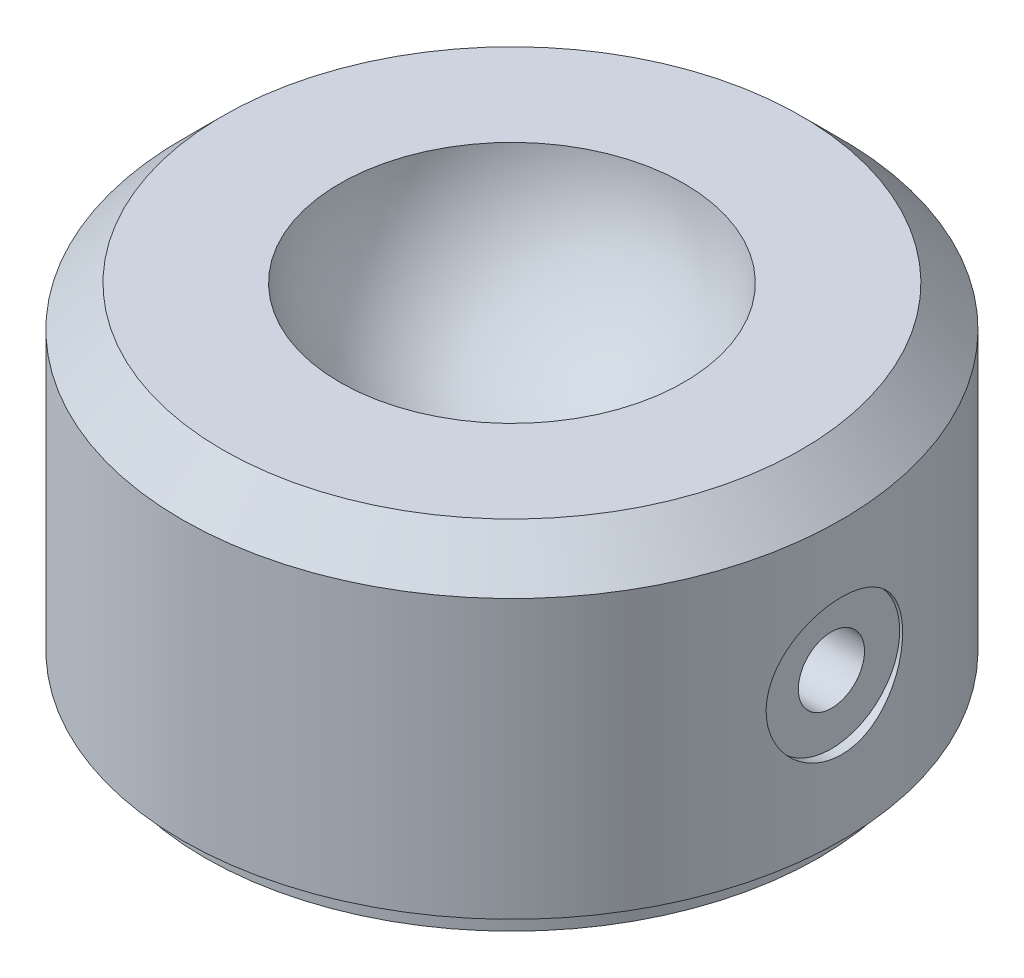
SolidWorks part; units mm, degrees
ref_plane "Front Plane" through (0, 0, 0) normal (0, 0, 1) x (1, 0, 0)
ref_plane "Top Plane" through (0, 0, 0) normal (0, 1, 0) x (1, 0, 0)
ref_plane "Right Plane" through (0, 0, 0) normal (1, 0, 0) x (0, 0, -1)
sketch "Sketch1" plane through (0, 0, 0) normal (0, 1, 0) x (1, 0, 0)
  circle A0 centre (0, 0) radius 12.446
  dimension "D1" = 24.892
extrude "Extrude1" add sketch "Sketch1" along normal mid plane 12.0142
chamfer "Chamfer1" distance 1.524 angle 45 1 edges at (0, 6.0071, 12.446)
sketch "Sketch2" plane through (0, -6.0071, 0) normal (0, -1, 0) x (1, 0, 0)
  circle A0 centre (0, 0) radius 11.5951
  dimension "D1" = 23.1902
extrude "Extrude2" add sketch "Sketch2" along normal blind 0.9908
sketch "Sketch3" plane through (0, 6.0071, 0) normal (0, 1, 0) x (1, 0, 0)
  circle A0 centre (0, 0) radius 1.5875
  dimension "D1" = 3.175
extrude "Extrude3" cut sketch "Sketch3" against normal blind 6.3754
sketch "Sketch4" plane through (0, 0, 0) normal (0, 0, 1) x (1, 0, 0)
  line L0 (0, 13.0351) -> (0, -0.0049)
  line L1 (10.922, 6.0071) -> (-10.922, 6.0071) construction
  arc A0 (0, 13.0351) -> (0, -0.0049) centre (0, 6.5151) cw
  dimension "D1" = 6.52
  dimension "D2" = 0.508
revolve "Cut-Revolve1" cut sketch "Sketch4" angle 360 about L0
ref_plane "Plane1" through (12.446, 0, 0) normal (1, 0, 0) x (0, 0, -1)
hole_wizard "5/16 (0.3125) Diameter Hole2" positions "Sketch7" profile "Sketch6" hole size "5/16" standard "Ansi Inch"
sketch "Sketch7" plane through (12.446, 0, 0) normal (1, 0, 0) x (0, 0, -1)
  line L0 (6.5002, 6.0071) -> (-6.5002, 6.0071) construction
  point P0 (0, -0.6223)
  dimension "D1" = 6.6294
sketch "Sketch6" plane through (12.446, -0.6223, 0) normal (0, 1, 0) x (0, 0, -1)
  line L0 (0, 0) -> (0, 0.381)
  line L1 (0, 0.381) -> (2.5781, 0.381)
  line L2 (2.5781, 0.381) -> (2.5781, 0)
  line L5 (2.5781, 0) -> (0, 0)
  line L10 (0, 0.381) -> (-2.5781, 0.381) construction
  line L11 (0, -6.35) -> (0, 107.95) construction
  dimension "Hole Dia." = 5.1562
  dimension "Hole Depth" = 0.381
  dimension "Drill Angle" = 180
hole_wizard "M3x0.5 Tapped Hole1" positions "Sketch9" profile "Sketch8" tap size "M3x0.5" standard "Ansi Metric"
sketch "Sketch9" plane through (12.065, 0, 0) normal (1, 0, 0) x (0, 0, -1)
  point P0 (0, -0.6223)
sketch "Sketch8" plane through (12.065, -0.6223, 0) normal (0, 1, 0) x (0, 0, -1)
  line L0 (0, 0) -> (0, 6.0597)
  line L1 (0, 6.0597) -> (1.25, 5.3086)
  line L2 (1.25, 5.3086) -> (1.25, 0)
  line L5 (1.25, 0) -> (0, 0)
  line L10 (0, 6.0597) -> (-1.25, 5.3086) construction
  line L11 (0, -6.35) -> (0, 107.95) construction
  dimension "Tap Drill Dia." = 2.5
  dimension "Tap Drill Depth" = 5.3086
  dimension "Drill Angle" = 118
cosmetic thread "Hole Thread1" parameters "D1"=3.81, "D2"=3
